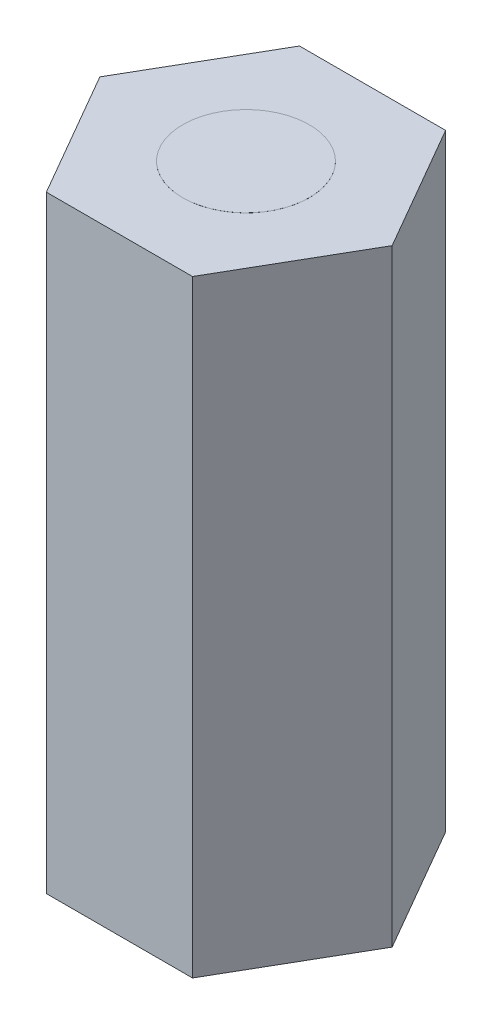
SolidWorks part; units mm, degrees
material "Brass"
ref_plane "Front Plane" through (0, 0, 0) normal (0, 0, 1) x (1, 0, 0)
ref_plane "Top Plane" through (0, 0, 0) normal (0, 1, 0) x (1, 0, 0)
ref_plane "Right Plane" through (0, 0, 0) normal (1, 0, 0) x (0, 0, -1)
sketch "Sketch1" plane through (0, 0, 0) normal (0, 1, 0) x (1, 0, 0)
  line L1 (-2.8868, 0) -> (-1.4434, -2.5)
  line L2 (-1.4434, -2.5) -> (1.4434, -2.5)
  line L3 (1.4434, -2.5) -> (2.8868, 0)
  line L4 (2.8868, 0) -> (1.4434, 2.5)
  line L5 (1.4434, 2.5) -> (-1.4434, 2.5)
  line L6 (-1.4434, 2.5) -> (-2.8868, 0)
  circle A0 centre (0, 0) radius 2.5 construction
  dimension "D1" = 5
extrude "Boss-Extrude1" add sketch "Sketch1" along normal blind 12
sketch "Sketch2" plane through (0, 12, 0) normal (0, 1, 0) x (1, 0, 0)
  circle A0 centre (0, 0) radius 1.25
  dimension "D1" = 2.5
extrude "Boss-Extrude2" add sketch "Sketch2" along normal blind 0.001
equation "\"Distance\"= 8mm"
